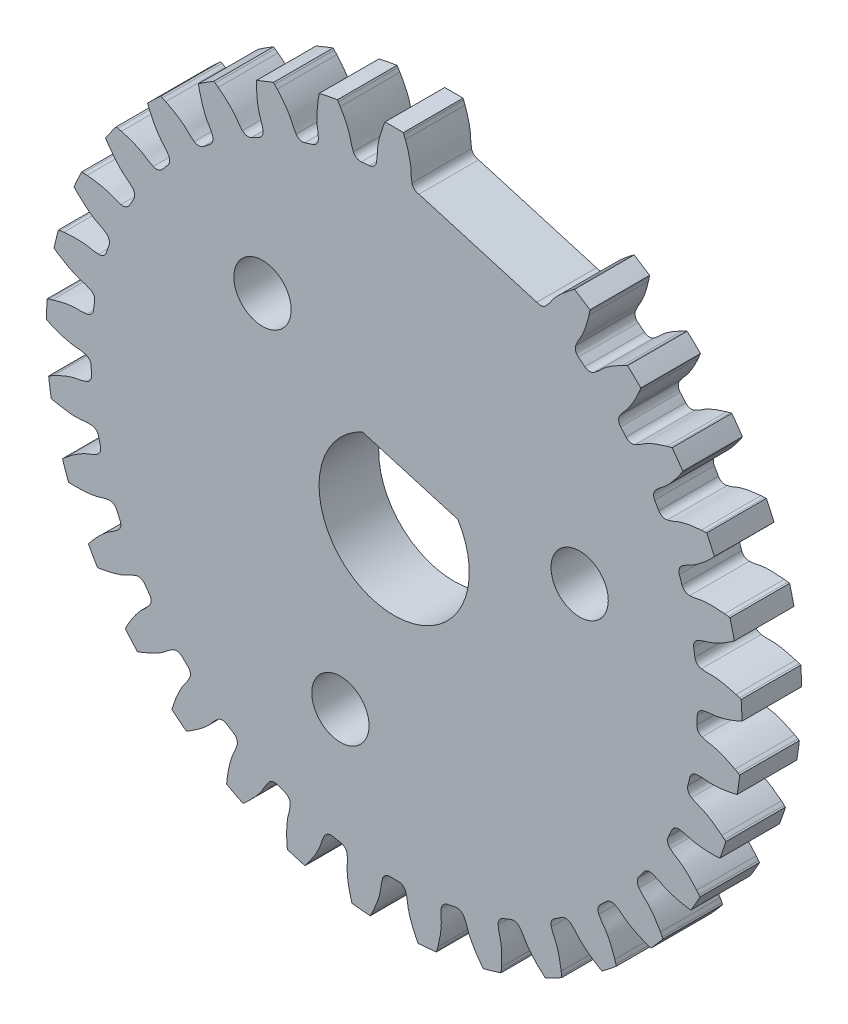
SolidWorks part; units mm, degrees
ref_plane "Front Plane" through (0, 0, 0) normal (0, 0, 1) x (1, 0, 0)
ref_plane "Top Plane" through (0, 0, 0) normal (0, 1, 0) x (1, 0, 0)
ref_plane "Right Plane" through (0, 0, 0) normal (1, 0, 0) x (0, 0, -1)
sketch "Sketch1" plane through (0, 0, 0) normal (0, 0, 1) x (1, 0, 0)
  line L0 (1.3177, 16.0878) -> (7.5892, 14.2464)
  line L1 (-1.6934, 3.6239) -> (3.3838, 2.1331)
  line L2 (-2.8624, -9.7484) -> (4.4535, 15.1671) construction
  arc A0 (-1.6934, 3.6239) -> (3.3838, 2.1331) centre (0, 0) ccw
  circle A1 centre (-2.8624, -9.7484) radius 1.524
  arc A2 (0.9461, 16.421) -> (1.3177, 16.0878) centre (1.3514, 16.4992) ccw
  circle A3 centre (-7.0112, 7.3531) radius 1.524
  arc A4 (7.5892, 14.2464) -> (8.0819, 14.3257) centre (7.7833, 14.6106) ccw
  arc A5 (9.6738, 13.3027) -> (9.8063, 12.8215) centre (10.057, 13.1494) ccw
  arc A6 (10.1482, 12.5526) -> (9.8063, 12.8215) centre (0, 0) ccw
  arc A7 (10.1482, 12.5526) -> (10.647, 12.5373) centre (10.4077, 12.8736) ccw
  arc A8 (12.0165, 11.2315) -> (12.0556, 10.734) centre (12.3638, 11.0084) ccw
  arc A9 (12.3404, 10.4052) -> (12.0556, 10.734) centre (0, 0) ccw
  arc A10 (12.3404, 10.4052) -> (12.8273, 10.2958) centre (12.6559, 10.6713) ccw
  arc A11 (13.925, 8.7544) -> (13.8691, 8.2585) centre (14.2237, 8.4696) ccw
  arc A12 (14.0866, 7.8818) -> (13.8691, 8.2585) centre (0, 0) ccw
  arc A13 (14.0866, 7.8818) -> (14.544, 7.6822) centre (14.4468, 8.0833) ccw
  arc A14 (15.3301, 5.9609) -> (15.1814, 5.4845) centre (15.5696, 5.6247) ccw
  arc A15 (15.3237, 5.0734) -> (15.1814, 5.4845) centre (0, 0) ccw
  arc A16 (15.3237, 5.0734) -> (15.735, 4.7909) centre (15.7155, 5.2032) ccw
  arc A17 (16.1812, 2.9519) -> (15.945, 2.5123) centre (16.3527, 2.5765) ccw
  arc A18 (16.0069, 2.0817) -> (15.945, 2.5123) centre (0, 0) ccw
  arc A19 (16.0069, 2.0817) -> (16.3574, 1.7264) centre (16.4162, 2.135) ccw
  arc A20 (16.4474, -0.1637) -> (16.1323, -0.5507) centre (16.5448, -0.5648) ccw
  arc A21 (16.1116, -0.9852) -> (16.1323, -0.5507) centre (0, 0) ccw
  arc A22 (16.1116, -0.9852) -> (16.3885, -1.4004) centre (16.5236, -1.0104) ccw
  arc A23 (16.1192, -3.2735) -> (15.7365, -3.5938) centre (16.1389, -3.6857) ccw
  arc A24 (15.634, -4.0166) -> (15.7365, -3.5938) centre (0, 0) ccw
  arc A25 (15.634, -4.0166) -> (15.8273, -4.4767) centre (16.0338, -4.1193) ccw
  arc A26 (15.2084, -6.2649) -> (14.772, -6.5071) centre (15.1497, -6.6734) ccw
  arc A27 (14.5913, -6.9027) -> (14.772, -6.5071) centre (0, 0) ccw
  arc A28 (14.5913, -6.9027) -> (14.6941, -7.3911) centre (14.9644, -7.0792) ccw
  arc A29 (13.7479, -9.0299) -> (13.2736, -9.1851) centre (13.613, -9.42) ccw
  arc A30 (13.0213, -9.5394) -> (13.2736, -9.1851) centre (0, 0) ccw
  arc A31 (13.0213, -9.5394) -> (13.0297, -10.0384) centre (13.3543, -9.7833) ccw
  arc A32 (11.7906, -11.4685) -> (11.2954, -11.5312) centre (11.5843, -11.826) ccw
  arc A33 (10.9806, -11.8313) -> (11.2954, -11.5312) centre (0, 0) ccw
  arc A34 (10.9806, -11.8313) -> (10.8945, -12.3229) centre (11.2614, -12.1339) ccw
  arc A35 (9.4071, -13.4926) -> (8.909, -13.4604) centre (9.1368, -13.8046) ccw
  arc A36 (8.5431, -13.6956) -> (8.909, -13.4604) centre (0, 0) ccw
  arc A37 (8.5431, -13.6956) -> (8.3655, -14.162) centre (8.7616, -14.0458) ccw
  arc A38 (6.6836, -15.0291) -> (6.2006, -14.9032) centre (6.3592, -15.2843) ccw
  arc A39 (5.7968, -15.0649) -> (6.2006, -14.9032) centre (0, 0) ccw
  arc A40 (5.7968, -15.0649) -> (5.5341, -15.4893) centre (5.945, -15.4501) ccw
  arc A41 (3.7185, -16.0224) -> (3.2681, -15.8074) centre (3.3517, -16.2116) ccw
  arc A42 (2.841, -15.8897) -> (3.2681, -15.8074) centre (0, 0) ccw
  arc A43 (2.841, -15.8897) -> (2.5028, -16.2567) centre (2.9136, -16.296) ccw
  arc A44 (0.6191, -16.4366) -> (0.2175, -16.1402) centre (0.2231, -16.5529) ccw
  arc A45 (-0.2175, -16.1402) -> (0.2175, -16.1402) centre (0, 0) ccw
  arc A46 (-0.2175, -16.1402) -> (-0.6191, -16.4366) centre (-0.2231, -16.5529) ccw
  arc A47 (-2.5028, -16.2567) -> (-2.841, -15.8897) centre (-2.9136, -16.296) ccw
  arc A48 (-3.2681, -15.8074) -> (-2.841, -15.8897) centre (0, 0) ccw
  arc A49 (-3.2681, -15.8074) -> (-3.7185, -16.0224) centre (-3.3517, -16.2116) ccw
  arc A50 (-5.5341, -15.4893) -> (-5.7968, -15.0649) centre (-5.945, -15.4501) ccw
  arc A51 (-6.2006, -14.9032) -> (-5.7968, -15.0649) centre (0, 0) ccw
  arc A52 (-6.2006, -14.9032) -> (-6.6836, -15.0291) centre (-6.3592, -15.2843) ccw
  arc A53 (-8.3655, -14.162) -> (-8.5431, -13.6956) centre (-8.7616, -14.0458) ccw
  arc A54 (-8.909, -13.4604) -> (-8.5431, -13.6956) centre (0, 0) ccw
  arc A55 (-8.909, -13.4604) -> (-9.4071, -13.4926) centre (-9.1368, -13.8046) ccw
  arc A56 (-10.8945, -12.3229) -> (-10.9806, -11.8313) centre (-11.2614, -12.1339) ccw
  arc A57 (-11.2954, -11.5312) -> (-10.9806, -11.8313) centre (0, 0) ccw
  arc A58 (-11.2954, -11.5312) -> (-11.7906, -11.4685) centre (-11.5843, -11.826) ccw
  arc A59 (-13.0297, -10.0384) -> (-13.0213, -9.5394) centre (-13.3543, -9.7833) ccw
  arc A60 (-13.2736, -9.1851) -> (-13.0213, -9.5394) centre (0, 0) ccw
  arc A61 (-13.2736, -9.1851) -> (-13.7479, -9.0299) centre (-13.613, -9.42) ccw
  arc A62 (-14.6941, -7.3911) -> (-14.5913, -6.9027) centre (-14.9644, -7.0792) ccw
  arc A63 (-14.772, -6.5071) -> (-14.5913, -6.9027) centre (0, 0) ccw
  arc A64 (-14.772, -6.5071) -> (-15.2084, -6.2649) centre (-15.1497, -6.6734) ccw
  arc A65 (-15.8273, -4.4767) -> (-15.634, -4.0166) centre (-16.0338, -4.1193) ccw
  arc A66 (-15.7365, -3.5938) -> (-15.634, -4.0166) centre (0, 0) ccw
  arc A67 (-15.7365, -3.5938) -> (-16.1192, -3.2735) centre (-16.1389, -3.6857) ccw
  arc A68 (-16.3885, -1.4004) -> (-16.1116, -0.9852) centre (-16.5236, -1.0104) ccw
  arc A69 (-16.1323, -0.5507) -> (-16.1116, -0.9852) centre (0, 0) ccw
  arc A70 (-16.1323, -0.5507) -> (-16.4474, -0.1637) centre (-16.5448, -0.5648) ccw
  arc A71 (-16.3574, 1.7264) -> (-16.0069, 2.0817) centre (-16.4162, 2.135) ccw
  arc A72 (-15.945, 2.5123) -> (-16.0069, 2.0817) centre (0, 0) ccw
  arc A73 (-15.945, 2.5123) -> (-16.1812, 2.9519) centre (-16.3527, 2.5765) ccw
  arc A74 (-15.735, 4.7909) -> (-15.3237, 5.0734) centre (-15.7155, 5.2032) ccw
  arc A75 (-15.1814, 5.4845) -> (-15.3237, 5.0734) centre (0, 0) ccw
  arc A76 (-15.1814, 5.4845) -> (-15.3301, 5.9609) centre (-15.5696, 5.6247) ccw
  arc A77 (-14.544, 7.6822) -> (-14.0866, 7.8818) centre (-14.4468, 8.0833) ccw
  arc A78 (-13.8691, 8.2585) -> (-14.0866, 7.8818) centre (0, 0) ccw
  arc A79 (-13.8691, 8.2585) -> (-13.925, 8.7544) centre (-14.2237, 8.4696) ccw
  arc A80 (-12.8273, 10.2958) -> (-12.3404, 10.4052) centre (-12.6559, 10.6713) ccw
  arc A81 (-12.0556, 10.734) -> (-12.3404, 10.4052) centre (0, 0) ccw
  arc A82 (-12.0556, 10.734) -> (-12.0165, 11.2315) centre (-12.3638, 11.0084) ccw
  arc A83 (-10.647, 12.5373) -> (-10.1482, 12.5526) centre (-10.4077, 12.8736) ccw
  arc A84 (-9.8063, 12.8215) -> (-10.1482, 12.5526) centre (0, 0) ccw
  arc A85 (-9.8063, 12.8215) -> (-9.6738, 13.3027) centre (-10.057, 13.1494) ccw
  arc A86 (-8.0819, 14.3257) -> (-7.5892, 14.2464) centre (-7.7833, 14.6106) ccw
  arc A87 (-7.2026, 14.4457) -> (-7.5892, 14.2464) centre (0, 0) ccw
  arc A88 (-7.2026, 14.4457) -> (-6.9814, 14.8931) centre (-7.3867, 14.8151) ccw
  arc A89 (-5.2247, 15.5964) -> (-4.7559, 15.4252) centre (-4.8775, 15.8196) ccw
  arc A90 (-4.3386, 15.5477) -> (-4.7559, 15.4252) centre (0, 0) ccw
  arc A91 (-4.3386, 15.5477) -> (-4.0367, 15.9452) centre (-4.4495, 15.9453) ccw
  arc A92 (-2.1786, 16.3033) -> (-1.7507, 16.0465) centre (-1.7955, 16.4568) ccw
  arc A93 (-1.3177, 16.0878) -> (-1.7507, 16.0465) centre (0, 0) ccw
  arc A94 (-1.3177, 16.0878) -> (-0.9461, 16.421) centre (-1.3514, 16.4992) ccw
  arc A95 (10.4216, 15.3105) -> (9.5977, 15.84) centre (0, 0) ccw
  arc A96 (-14.3129, -11.7542) -> (-13.6715, -12.4944) centre (0, 0) ccw
  arc A97 (-16.6378, 8.1366) -> (-17.0447, 7.2457) centre (0, 0) ccw
  arc A98 (17.0447, 7.2457) -> (16.6378, 8.1366) centre (0, 0) ccw
  arc A99 (11.0599, -14.856) -> (11.8297, -14.2506) centre (0, 0) ccw
  arc A100 (-18.3956, -2.1502) -> (-18.2562, -3.1196) centre (0, 0) ccw
  arc A101 (17.3359, -6.5182) -> (17.6562, -5.5927) centre (0, 0) ccw
  arc A102 (4.7462, -17.9024) -> (5.6859, -17.6264) centre (0, 0) ccw
  arc A103 (18.1079, 3.889) -> (17.877, 4.8408) centre (0, 0) ccw
  arc A104 (-12.422, 13.7374) -> (-13.1308, 13.0615) centre (0, 0) ccw
  arc A105 (-17.877, 4.8408) -> (-18.1079, 3.889) centre (0, 0) ccw
  arc A106 (-9.5977, 15.84) -> (-10.4216, 15.3105) centre (0, 0) ccw
  arc A107 (-5.6859, -17.6264) -> (-4.7462, -17.9024) centre (0, 0) ccw
  arc A108 (0.4897, 18.5144) -> (-0.4897, 18.5144) centre (0, 0) ccw
  arc A109 (-11.8297, -14.2506) -> (-11.0599, -14.856) centre (0, 0) ccw
  arc A110 (-16.2787, -8.8331) -> (-15.7891, -9.6813) centre (0, 0) ccw
  arc A111 (1.2724, -18.4771) -> (2.2474, -18.384) centre (0, 0) ccw
  arc A112 (-3.023, 18.2725) -> (-3.9847, 18.0871) centre (0, 0) ccw
  arc A113 (18.5167, 0.3918) -> (18.4701, 1.3701) centre (0, 0) ccw
  arc A114 (13.1308, 13.0615) -> (12.422, 13.7374) centre (0, 0) ccw
  arc A115 (8.0485, -16.6806) -> (8.919, -16.2318) centre (0, 0) ccw
  arc A116 (13.6715, -12.4944) -> (14.3129, -11.7542) centre (0, 0) ccw
  arc A117 (-18.4701, 1.3701) -> (-18.5167, 0.3918) centre (0, 0) ccw
  arc A118 (-2.2474, -18.384) -> (-1.2724, -18.4771) centre (0, 0) ccw
  arc A119 (15.3654, 10.3405) -> (14.7973, 11.1383) centre (0, 0) ccw
  arc A120 (-8.919, -16.2318) -> (-8.0485, -16.6806) centre (0, 0) ccw
  arc A121 (15.7891, -9.6813) -> (16.2787, -8.8331) centre (0, 0) ccw
  arc A122 (-14.7973, 11.1383) -> (-15.3654, 10.3405) centre (0, 0) ccw
  arc A123 (-17.6562, -5.5927) -> (-17.3359, -6.5182) centre (0, 0) ccw
  arc A124 (18.2562, -3.1196) -> (18.3956, -2.1502) centre (0, 0) ccw
  arc A125 (-6.4265, 17.3701) -> (-7.3357, 17.0061) centre (0, 0) ccw
  circle A126 centre (9.8736, 2.3953) radius 1.524
  spline S31 degree 3 poles (-11.7906, -11.4685) (-11.8581, -11.5075) (-11.9247, -11.5479) (-12.0526, -11.6363) (-12.1128, -11.6859) (-12.2326, -11.7859) (-12.2929, -11.8353) (-12.421, -11.9234) (-12.4877, -11.9637) (-12.8258, -12.1584) (-13.1079, -12.2893) (-13.4001, -12.3987) knots 0 0 0 0 0.125 0.125 0.25 0.25 0.375 0.375 0.5 0.5 1 1 1 1
  spline S32 degree 3 poles (-6.6836, -15.0291) (-6.7318, -15.0904) (-6.7786, -15.1527) (-6.8644, -15.2823) (-6.9019, -15.3507) (-6.9759, -15.4881) (-7.0136, -15.5563) (-7.0998, -15.6857) (-7.1467, -15.7479) (-7.3882, -16.0543) (-7.6014, -16.2807) (-7.8321, -16.4909) knots 0 0 0 0 0.125 0.125 0.25 0.25 0.375 0.375 0.5 0.5 1 1 1 1
  spline S33 degree 3 poles (-3.7185, -16.0224) (-3.7543, -16.0917) (-3.7885, -16.1617) (-3.8482, -16.3052) (-3.872, -16.3795) (-3.9187, -16.5284) (-3.9428, -16.6025) (-4.0029, -16.7459) (-4.0372, -16.8158) (-4.2164, -17.1624) (-4.3829, -17.4251) (-4.5696, -17.6751) knots 0 0 0 0 0.125 0.125 0.25 0.25 0.375 0.375 0.5 0.5 1 1 1 1
  spline S34 degree 3 poles (-16.1812, 2.9519) (-16.2521, 2.9843) (-16.3237, 3.0152) (-16.4699, 3.068) (-16.5452, 3.0883) (-16.6961, 3.1278) (-16.7713, 3.1484) (-16.9174, 3.2016) (-16.9889, 3.2325) (-17.3436, 3.395) (-17.6139, 3.5488) (-17.8725, 3.7234) knots 0 0 0 0 0.125 0.125 0.25 0.25 0.375 0.375 0.5 0.5 1 1 1 1
  spline S35 degree 3 poles (-4.0367, 15.9452) (-4.0367, 16.0232) (-4.0384, 16.1011) (-4.0511, 16.256) (-4.0639, 16.3329) (-4.0906, 16.4867) (-4.1032, 16.5636) (-4.1155, 16.7186) (-4.117, 16.7965) (-4.1166, 17.1866) (-4.0889, 17.4964) (-4.0376, 17.8042) knots 0 0 0 0 0.125 0.125 0.25 0.25 0.375 0.375 0.5 0.5 1 1 1 1
  spline S36 degree 3 poles (-16.1192, -3.2735) (-16.1971, -3.2697) (-16.275, -3.2677) (-16.4304, -3.273) (-16.5078, -3.2821) (-16.6626, -3.3015) (-16.7401, -3.3104) (-16.8955, -3.3153) (-16.9733, -3.3132) (-17.363, -3.2941) (-17.6712, -3.2518) (-17.9761, -3.1858) knots 0 0 0 0 0.125 0.125 0.25 0.25 0.375 0.375 0.5 0.5 1 1 1 1
  spline S37 degree 3 poles (-16.4474, -0.1637) (-16.5232, -0.1453) (-16.5993, -0.1286) (-16.7529, -0.1044) (-16.8306, -0.0987) (-16.9863, -0.0884) (-17.0641, -0.0825) (-17.2176, -0.0579) (-17.2936, -0.0411) (-17.6727, 0.0514) (-17.9672, 0.1513) (-18.2542, 0.2737) knots 0 0 0 0 0.125 0.125 0.25 0.25 0.375 0.375 0.5 0.5 1 1 1 1
  spline S38 degree 3 poles (-15.3301, 5.9609) (-15.3936, 6.0062) (-15.4581, 6.0499) (-15.5916, 6.1295) (-15.6617, 6.1637) (-15.8024, 6.2311) (-15.8724, 6.2655) (-16.0058, 6.3454) (-16.0701, 6.3893) (-16.3876, 6.616) (-16.624, 6.8182) (-16.8449, 7.0385) knots 0 0 0 0 0.125 0.125 0.25 0.25 0.375 0.375 0.5 0.5 1 1 1 1
  spline S39 degree 3 poles (5.5341, -15.4893) (5.5415, -15.5669) (5.5506, -15.6443) (5.578, -15.7973) (5.598, -15.8727) (5.6393, -16.0232) (5.6591, -16.0986) (5.686, -16.2517) (5.695, -16.3291) (5.7316, -16.7175) (5.7336, -17.0285) (5.7117, -17.3398) knots 0 0 0 0 0.125 0.125 0.25 0.25 0.375 0.375 0.5 0.5 1 1 1 1
  spline S40 degree 3 poles (14.6941, -7.3911) (14.753, -7.4422) (14.813, -7.4919) (14.9384, -7.5838) (15.0049, -7.6245) (15.1386, -7.705) (15.205, -7.7459) (15.3301, -7.8381) (15.39, -7.8879) (15.6846, -8.1438) (15.9006, -8.3675) (16.0995, -8.6079) knots 0 0 0 0 0.125 0.125 0.25 0.25 0.375 0.375 0.5 0.5 1 1 1 1
  spline S41 degree 3 poles (2.5028, -16.2567) (2.4953, -16.3344) (2.4896, -16.412) (2.4875, -16.5675) (2.493, -16.6453) (2.505, -16.8009) (2.5102, -16.8786) (2.5076, -17.0341) (2.5018, -17.1118) (2.4642, -17.5001) (2.4073, -17.8059) (2.3269, -18.1074) knots 0 0 0 0 0.125 0.125 0.25 0.25 0.375 0.375 0.5 0.5 1 1 1 1
  spline S42 degree 3 poles (12.8273, 10.2958) (12.8983, 10.3282) (12.9684, 10.3621) (13.1041, 10.438) (13.1688, 10.4816) (13.2975, 10.5698) (13.3623, 10.6132) (13.4981, 10.6887) (13.5683, 10.7225) (13.9234, 10.8841) (14.2167, 10.9877) (14.518, 11.0688) knots 0 0 0 0 0.125 0.125 0.25 0.25 0.375 0.375 0.5 0.5 1 1 1 1
  spline S43 degree 3 poles (8.3655, -14.162) (8.3875, -14.2369) (8.411, -14.3111) (8.4668, -14.4562) (8.5008, -14.5264) (8.5698, -14.6664) (8.6035, -14.7367) (8.6589, -14.8819) (8.6824, -14.9562) (8.7918, -15.3307) (8.8526, -15.6357) (8.89, -15.9455) knots 0 0 0 0 0.125 0.125 0.25 0.25 0.375 0.375 0.5 0.5 1 1 1 1
  spline S44 degree 3 poles (-13.925, 8.7544) (-13.9788, 8.8109) (-14.0338, 8.8661) (-14.1498, 8.9695) (-14.2122, 9.0163) (-14.3376, 9.1091) (-14.3998, 9.1561) (-14.5157, 9.2598) (-14.5705, 9.3151) (-14.8394, 9.5978) (-15.0332, 9.8411) (-15.2084, 10.0992) knots 0 0 0 0 0.125 0.125 0.25 0.25 0.375 0.375 0.5 0.5 1 1 1 1
  spline S45 degree 3 poles (10.647, 12.5373) (10.7106, 12.5826) (10.773, 12.6291) (10.8919, 12.7293) (10.9471, 12.7844) (11.0568, 12.8953) (11.1122, 12.9502) (11.2314, 13.0501) (11.2939, 13.0966) (11.612, 13.3225) (11.8803, 13.4797) (12.1608, 13.6163) knots 0 0 0 0 0.125 0.125 0.25 0.25 0.375 0.375 0.5 0.5 1 1 1 1
  spline S46 degree 3 poles (-0.6191, -16.4366) (-0.6411, -16.5114) (-0.6614, -16.5866) (-0.6929, -16.7389) (-0.7022, -16.8163) (-0.7199, -16.9713) (-0.7295, -17.0487) (-0.7614, -17.2008) (-0.7818, -17.276) (-0.8922, -17.6502) (-1.006, -17.9397) (-1.142, -18.2205) knots 0 0 0 0 0.125 0.125 0.25 0.25 0.375 0.375 0.5 0.5 1 1 1 1
  spline S47 degree 3 poles (15.735, 4.7909) (15.813, 4.7946) (15.8907, 4.8) (16.0449, 4.82) (16.1211, 4.8365) (16.2734, 4.8705) (16.3496, 4.8867) (16.5038, 4.9063) (16.5816, 4.9116) (16.9713, 4.9297) (17.282, 4.9168) (17.5919, 4.8802) knots 0 0 0 0 0.125 0.125 0.25 0.25 0.375 0.375 0.5 0.5 1 1 1 1
  spline S48 degree 3 poles (-6.9814, 14.8931) (-6.9962, 14.9697) (-7.0126, 15.0458) (-7.0543, 15.1956) (-7.0815, 15.2687) (-7.1368, 15.4146) (-7.1637, 15.4877) (-7.2051, 15.6376) (-7.2214, 15.7138) (-7.2948, 16.097) (-7.3263, 16.4064) (-7.3341, 16.7183) knots 0 0 0 0 0.125 0.125 0.25 0.25 0.375 0.375 0.5 0.5 1 1 1 1
  spline S49 degree 3 poles (-13.7479, -9.0299) (-13.8217, -9.0554) (-13.8947, -9.0825) (-14.037, -9.1451) (-14.1055, -9.1824) (-14.242, -9.2579) (-14.3106, -9.295) (-14.453, -9.3572) (-14.5261, -9.3842) (-14.895, -9.5113) (-15.1968, -9.5866) (-15.5044, -9.6387) knots 0 0 0 0 0.125 0.125 0.25 0.25 0.375 0.375 0.5 0.5 1 1 1 1
  spline S50 degree 3 poles (16.3885, -1.4004) (16.4622, -1.426) (16.5364, -1.4498) (16.6869, -1.4886) (16.7638, -1.5016) (16.9178, -1.5266) (16.9947, -1.5399) (17.1451, -1.579) (17.2192, -1.603) (17.5878, -1.731) (17.8715, -1.8585) (18.1455, -2.0077) knots 0 0 0 0 0.125 0.125 0.25 0.25 0.375 0.375 0.5 0.5 1 1 1 1
  spline S51 degree 3 poles (14.544, 7.6822) (14.6198, 7.7005) (14.6951, 7.7206) (14.8427, 7.7694) (14.9144, 7.8) (15.0575, 7.8622) (15.1293, 7.8926) (15.2771, 7.941) (15.3524, 7.9609) (15.7316, 8.0524) (16.0392, 8.0986) (16.3504, 8.1213) knots 0 0 0 0 0.125 0.125 0.25 0.25 0.375 0.375 0.5 0.5 1 1 1 1
  spline S52 degree 3 poles (16.3574, 1.7264) (16.4346, 1.7153) (16.5119, 1.7059) (16.6671, 1.6964) (16.745, 1.6981) (16.901, 1.7027) (16.979, 1.7042) (17.1341, 1.6943) (17.2114, 1.6847) (17.5975, 1.6288) (17.9002, 1.5573) (18.1976, 1.4627) knots 0 0 0 0 0.125 0.125 0.25 0.25 0.375 0.375 0.5 0.5 1 1 1 1
  spline S53 degree 3 poles (-9.4071, -13.4926) (-9.466, -13.5437) (-9.5238, -13.596) (-9.6326, -13.707) (-9.6823, -13.7671) (-9.781, -13.888) (-9.8309, -13.9479) (-9.94, -14.0586) (-9.9978, -14.1108) (-10.293, -14.3659) (-10.5452, -14.5479) (-10.8114, -14.7107) knots 0 0 0 0 0.125 0.125 0.25 0.25 0.375 0.375 0.5 0.5 1 1 1 1
  spline S54 degree 3 poles (-9.6738, 13.3027) (-9.7028, 13.3751) (-9.7333, 13.4468) (-9.8026, 13.5859) (-9.8431, 13.6526) (-9.9251, 13.7854) (-9.9654, 13.8521) (-10.0343, 13.9914) (-10.0647, 14.0632) (-10.2093, 14.4255) (-10.2988, 14.7234) (-10.3655, 15.0282) knots 0 0 0 0 0.125 0.125 0.25 0.25 0.375 0.375 0.5 0.5 1 1 1 1
  spline S55 degree 3 poles (13.0297, -10.0384) (13.078, -10.0998) (13.1274, -10.1599) (13.2332, -10.2739) (13.2908, -10.3264) (13.4068, -10.4307) (13.4643, -10.4834) (13.5697, -10.5977) (13.6191, -10.6579) (13.8599, -10.9649) (14.0297, -11.2255) (14.1796, -11.4992) knots 0 0 0 0 0.125 0.125 0.25 0.25 0.375 0.375 0.5 0.5 1 1 1 1
  spline S56 degree 3 poles (-12.0165, 11.2315) (-12.0587, 11.2972) (-12.1022, 11.3618) (-12.1967, 11.4853) (-12.249, 11.543) (-12.3546, 11.6579) (-12.4068, 11.7158) (-12.5009, 11.8396) (-12.5443, 11.9043) (-12.7549, 12.2327) (-12.8991, 12.5083) (-13.0223, 12.7949) knots 0 0 0 0 0.125 0.125 0.25 0.25 0.375 0.375 0.5 0.5 1 1 1 1
  spline S57 degree 3 poles (-15.2084, -6.2649) (-15.2856, -6.276) (-15.3625, -6.2887) (-15.514, -6.3233) (-15.5883, -6.347) (-15.7367, -6.3953) (-15.8111, -6.4187) (-15.9627, -6.4529) (-16.0396, -6.4655) (-16.4258, -6.5206) (-16.7364, -6.5373) (-17.0483, -6.5303) knots 0 0 0 0 0.125 0.125 0.25 0.25 0.375 0.375 0.5 0.5 1 1 1 1
  spline S58 degree 3 poles (15.8273, -4.4767) (15.8949, -4.5157) (15.9631, -4.5532) (16.1037, -4.6197) (16.1767, -4.647) (16.3232, -4.7007) (16.3961, -4.7283) (16.5365, -4.7952) (16.6047, -4.8328) (16.9423, -5.0283) (17.1968, -5.2071) (17.4377, -5.4054) knots 0 0 0 0 0.125 0.125 0.25 0.25 0.375 0.375 0.5 0.5 1 1 1 1
  spline S59 degree 3 poles (10.8945, -12.3229) (10.9302, -12.3923) (10.9674, -12.4607) (11.0497, -12.5926) (11.0963, -12.6551) (11.1905, -12.7795) (11.237, -12.8421) (11.3189, -12.9743) (11.356, -13.0428) (11.5343, -13.3898) (11.6517, -13.6778) (11.7471, -13.9749) knots 0 0 0 0 0.125 0.125 0.25 0.25 0.375 0.375 0.5 0.5 1 1 1 1
  spline S60 degree 3 poles (8.0819, 14.3257) (8.1358, 14.3822) (8.1883, 14.4397) (8.286, 14.5606) (8.3298, 14.6251) (8.4166, 14.7548) (8.4606, 14.8192) (8.5586, 14.9398) (8.6113, 14.9973) (8.8808, 15.2793) (9.1146, 15.4844) (9.3642, 15.6717) knots 0 0 0 0 0.125 0.125 0.25 0.25 0.375 0.375 0.5 0.5 1 1 1 1
  spline S61 degree 3 poles (-6.229, 17.1607) (-6.0194, 16.9296) (-5.8286, 16.6837) (-5.6173, 16.3559) (-5.5766, 16.2895) (-5.5031, 16.1525) (-5.4721, 16.081) (-5.4115, 15.9372) (-5.3807, 15.8656) (-5.3076, 15.7284) (-5.2669, 15.662) (-5.2247, 15.5964) knots 0 0 0 0 0.5 0.5 0.625 0.625 0.75 0.75 0.875 0.875 1 1 1 1
  spline S62 degree 3 poles (-9.3642, 15.6717) (-9.1146, 15.4844) (-8.8807, 15.2792) (-8.6112, 14.9972) (-8.5586, 14.9398) (-8.4605, 14.8191) (-8.4165, 14.7548) (-8.3298, 14.6251) (-8.286, 14.5606) (-8.1883, 14.4397) (-8.1358, 14.3822) (-8.0819, 14.3257) knots 0 0 0 0 0.5 0.5 0.625 0.625 0.75 0.75 0.875 0.875 1 1 1 1
  spline S63 degree 3 poles (-11.7471, -13.9749) (-11.6517, -13.6778) (-11.5342, -13.3896) (-11.3559, -13.0427) (-11.3188, -12.9742) (-11.2369, -12.8421) (-11.1905, -12.7795) (-11.0963, -12.6551) (-11.0497, -12.5926) (-10.9674, -12.4607) (-10.9302, -12.3922) (-10.8945, -12.3229) knots 0 0 0 0 0.5 0.5 0.625 0.625 0.75 0.75 0.875 0.875 1 1 1 1
  spline S64 degree 3 poles (-8.89, -15.9455) (-8.8526, -15.6357) (-8.7918, -15.3305) (-8.6824, -14.9561) (-8.6589, -14.8818) (-8.6035, -14.7366) (-8.5697, -14.6663) (-8.5008, -14.5264) (-8.4668, -14.4562) (-8.411, -14.3111) (-8.3875, -14.2369) (-8.3655, -14.162) knots 0 0 0 0 0.5 0.5 0.625 0.625 0.75 0.75 0.875 0.875 1 1 1 1
  spline S65 degree 3 poles (-16.0995, -8.6079) (-15.9006, -8.3675) (-15.6844, -8.1436) (-15.39, -7.8878) (-15.3301, -7.838) (-15.2049, -7.7458) (-15.1385, -7.705) (-15.0049, -7.6245) (-14.9383, -7.5838) (-14.813, -7.4919) (-14.753, -7.4422) (-14.6941, -7.3911) knots 0 0 0 0 0.5 0.5 0.625 0.625 0.75 0.75 0.875 0.875 1 1 1 1
  spline S66 degree 3 poles (16.8449, 7.0385) (16.624, 6.8182) (16.3875, 6.6159) (16.0701, 6.3892) (16.0057, 6.3453) (15.8724, 6.2654) (15.8024, 6.2311) (15.6617, 6.1637) (15.5916, 6.1295) (15.458, 6.0499) (15.3936, 6.0061) (15.3301, 5.9609) knots 0 0 0 0 0.5 0.5 0.625 0.625 0.75 0.75 0.875 0.875 1 1 1 1
  spline S67 degree 3 poles (-14.518, 11.0688) (-14.2167, 10.9877) (-13.9233, 10.8841) (-13.5683, 10.7225) (-13.4981, 10.6887) (-13.3622, 10.6132) (-13.2975, 10.5698) (-13.1687, 10.4816) (-13.1041, 10.438) (-12.9684, 10.3621) (-12.8983, 10.3282) (-12.8273, 10.2958) knots 0 0 0 0 0.5 0.5 0.625 0.625 0.75 0.75 0.875 0.875 1 1 1 1
  spline S68 degree 3 poles (-5.7117, -17.3398) (-5.7336, -17.0285) (-5.7316, -16.7173) (-5.695, -16.329) (-5.686, -16.2516) (-5.6591, -16.0985) (-5.6393, -16.0231) (-5.598, -15.8726) (-5.578, -15.7973) (-5.5506, -15.6443) (-5.5415, -15.5669) (-5.5341, -15.4893) knots 0 0 0 0 0.5 0.5 0.625 0.625 0.75 0.75 0.875 0.875 1 1 1 1
  spline S69 degree 3 poles (-14.1796, -11.4992) (-14.0297, -11.2255) (-13.8598, -10.9648) (-13.6191, -10.6579) (-13.5697, -10.5976) (-13.4642, -10.4834) (-13.4068, -10.4307) (-13.2908, -10.3264) (-13.2331, -10.2739) (-13.1274, -10.1599) (-13.078, -10.0997) (-13.0297, -10.0384) knots 0 0 0 0 0.5 0.5 0.625 0.625 0.75 0.75 0.875 0.875 1 1 1 1
  spline S70 degree 3 poles (-17.5919, 4.8802) (-17.282, 4.9168) (-16.9711, 4.9297) (-16.5815, 4.9116) (-16.5038, 4.9063) (-16.3496, 4.8867) (-16.2733, 4.8705) (-16.121, 4.8364) (-16.0448, 4.82) (-15.8907, 4.8) (-15.813, 4.7946) (-15.735, 4.7909) knots 0 0 0 0 0.5 0.5 0.625 0.625 0.75 0.75 0.875 0.875 1 1 1 1
  spline S71 degree 3 poles (7.8321, -16.4909) (7.6014, -16.2807) (7.3881, -16.0542) (7.1466, -15.7478) (7.0997, -15.6857) (7.0136, -15.5563) (6.9759, -15.488) (6.9019, -15.3507) (6.8644, -15.2823) (6.7786, -15.1527) (6.7318, -15.0904) (6.6836, -15.0291) knots 0 0 0 0 0.5 0.5 0.625 0.625 0.75 0.75 0.875 0.875 1 1 1 1
  spline S72 degree 3 poles (-16.3504, 8.1213) (-16.0392, 8.0986) (-15.7315, 8.0524) (-15.3523, 7.9609) (-15.277, 7.941) (-15.1293, 7.8925) (-15.0575, 7.8622) (-14.9144, 7.8) (-14.8427, 7.7694) (-14.6951, 7.7205) (-14.6198, 7.7005) (-14.544, 7.6822) knots 0 0 0 0 0.5 0.5 0.625 0.625 0.75 0.75 0.875 0.875 1 1 1 1
  spline S73 degree 3 poles (10.8114, -14.7107) (10.5452, -14.5479) (10.2929, -14.3658) (9.9978, -14.1107) (9.94, -14.0586) (9.8309, -13.9478) (9.781, -13.8879) (9.6823, -13.7671) (9.6326, -13.707) (9.5238, -13.596) (9.466, -13.5437) (9.4071, -13.4926) knots 0 0 0 0 0.5 0.5 0.625 0.625 0.75 0.75 0.875 0.875 1 1 1 1
  spline S74 degree 3 poles (-17.4377, -5.4054) (-17.1968, -5.2071) (-16.9422, -5.0282) (-16.6046, -4.8327) (-16.5364, -4.7952) (-16.3961, -4.7283) (-16.3231, -4.7007) (-16.1766, -4.647) (-16.1036, -4.6197) (-15.9631, -4.5532) (-15.8948, -4.5157) (-15.8273, -4.4767) knots 0 0 0 0 0.5 0.5 0.625 0.625 0.75 0.75 0.875 0.875 1 1 1 1
  spline S75 degree 3 poles (18.2542, 0.2737) (17.9672, 0.1513) (17.6725, 0.0513) (17.2936, -0.0411) (17.2175, -0.0579) (17.064, -0.0825) (16.9863, -0.0885) (16.8306, -0.0987) (16.7528, -0.1044) (16.5993, -0.1286) (16.5232, -0.1453) (16.4474, -0.1637) knots 0 0 0 0 0.5 0.5 0.625 0.625 0.75 0.75 0.875 0.875 1 1 1 1
  spline S76 degree 3 poles (13.0223, 12.7949) (12.8991, 12.5083) (12.7548, 12.2326) (12.5443, 11.9042) (12.5009, 11.8395) (12.4068, 11.7158) (12.3546, 11.6579) (12.249, 11.543) (12.1966, 11.4852) (12.1022, 11.3617) (12.0587, 11.2971) (12.0165, 11.2315) knots 0 0 0 0 0.5 0.5 0.625 0.625 0.75 0.75 0.875 0.875 1 1 1 1
  spline S77 degree 3 poles (-2.3269, -18.1074) (-2.4073, -17.8059) (-2.4643, -17.4999) (-2.5018, -17.1117) (-2.5076, -17.034) (-2.5102, -16.8786) (-2.505, -16.8008) (-2.493, -16.6452) (-2.4875, -16.5674) (-2.4896, -16.412) (-2.4953, -16.3343) (-2.5028, -16.2567) knots 0 0 0 0 0.5 0.5 0.625 0.625 0.75 0.75 0.875 0.875 1 1 1 1
  spline S78 degree 3 poles (17.9761, -3.1858) (17.6711, -3.2518) (17.3629, -3.2941) (16.9733, -3.3132) (16.8954, -3.3153) (16.74, -3.3104) (16.6626, -3.3015) (16.5078, -3.2821) (16.4303, -3.273) (16.275, -3.2677) (16.1971, -3.2697) (16.1192, -3.2735) knots 0 0 0 0 0.5 0.5 0.625 0.625 0.75 0.75 0.875 0.875 1 1 1 1
  spline S79 degree 3 poles (-18.1976, 1.4627) (-17.9002, 1.5573) (-17.5974, 1.6288) (-17.2113, 1.6848) (-17.134, 1.6943) (-16.9789, 1.7042) (-16.901, 1.7027) (-16.745, 1.6981) (-16.667, 1.6964) (-16.5119, 1.7059) (-16.4346, 1.7153) (-16.3574, 1.7264) knots 0 0 0 0 0.5 0.5 0.625 0.625 0.75 0.75 0.875 0.875 1 1 1 1
  spline S80 degree 3 poles (-12.1608, 13.6163) (-11.8803, 13.4797) (-11.6118, 13.3224) (-11.2938, 13.0965) (-11.2313, 13.0501) (-11.1122, 12.9502) (-11.0568, 12.8953) (-10.9471, 12.7844) (-10.8919, 12.7293) (-10.773, 12.6291) (-10.7106, 12.5826) (-10.647, 12.5373) knots 0 0 0 0 0.5 0.5 0.625 0.625 0.75 0.75 0.875 0.875 1 1 1 1
  spline S81 degree 3 poles (1.142, -18.2205) (1.006, -17.9397) (0.8922, -17.65) (0.7818, -17.2759) (0.7614, -17.2008) (0.7295, -17.0486) (0.7199, -16.9713) (0.7022, -16.8162) (0.6929, -16.7388) (0.6614, -16.5866) (0.641, -16.5114) (0.6191, -16.4366) knots 0 0 0 0 0.5 0.5 0.625 0.625 0.75 0.75 0.875 0.875 1 1 1 1
  spline S82 degree 3 poles (-18.1455, -2.0077) (-17.8715, -1.8585) (-17.5876, -1.731) (-17.2192, -1.603) (-17.1451, -1.579) (-16.9946, -1.5399) (-16.9178, -1.5266) (-16.7638, -1.5016) (-16.6869, -1.4885) (-16.5363, -1.4498) (-16.4622, -1.426) (-16.3885, -1.4004) knots 0 0 0 0 0.5 0.5 0.625 0.625 0.75 0.75 0.875 0.875 1 1 1 1
  spline S83 degree 3 poles (15.2084, 10.0992) (15.0332, 9.8411) (14.8393, 9.5977) (14.5705, 9.315) (14.5156, 9.2598) (14.3998, 9.1561) (14.3376, 9.1091) (14.2122, 9.0163) (14.1498, 8.9694) (14.0337, 8.866) (13.9788, 8.8109) (13.925, 8.7544) knots 0 0 0 0 0.5 0.5 0.625 0.625 0.75 0.75 0.875 0.875 1 1 1 1
  spline S84 degree 3 poles (10.3655, 15.0282) (10.2988, 14.7234) (10.2092, 14.4254) (10.0647, 14.0631) (10.0343, 13.9914) (9.9653, 13.8521) (9.9251, 13.7853) (9.8431, 13.6525) (9.8026, 13.5859) (9.7333, 13.4468) (9.7028, 13.3751) (9.6738, 13.3027) knots 0 0 0 0 0.5 0.5 0.625 0.625 0.75 0.75 0.875 0.875 1 1 1 1
  spline S85 degree 3 poles (4.5696, -17.6751) (4.3829, -17.4251) (4.2163, -17.1622) (4.0372, -16.8158) (4.0029, -16.7458) (3.9428, -16.6025) (3.9187, -16.5283) (3.872, -16.3794) (3.8482, -16.3052) (3.7884, -16.1617) (3.7543, -16.0917) (3.7185, -16.0224) knots 0 0 0 0 0.5 0.5 0.625 0.625 0.75 0.75 0.875 0.875 1 1 1 1
  spline S86 degree 3 poles (0.5951, 18.2465) (0.7038, 17.9541) (0.7896, 17.6549) (0.8639, 17.272) (0.8771, 17.1953) (0.8944, 17.0408) (0.8966, 16.9628) (0.8994, 16.8068) (0.9014, 16.7289) (0.9183, 16.5744) (0.9314, 16.4976) (0.9461, 16.421) knots 0 0 0 0 0.5 0.5 0.625 0.625 0.75 0.75 0.875 0.875 1 1 1 1
  spline S87 degree 3 poles (17.0483, -6.5303) (16.7364, -6.5373) (16.4257, -6.5206) (16.0395, -6.4655) (15.9627, -6.4529) (15.811, -6.4187) (15.7367, -6.3953) (15.5883, -6.3469) (15.514, -6.3233) (15.3624, -6.2887) (15.2856, -6.276) (15.2084, -6.2649) knots 0 0 0 0 0.5 0.5 0.625 0.625 0.75 0.75 0.875 0.875 1 1 1 1
  spline S88 degree 3 poles (15.5044, -9.6387) (15.1968, -9.5866) (14.8948, -9.5113) (14.5261, -9.3842) (14.453, -9.3572) (14.3105, -9.2949) (14.242, -9.2579) (14.1054, -9.1823) (14.0369, -9.1451) (13.8947, -9.0824) (13.8216, -9.0554) (13.7479, -9.0299) knots 0 0 0 0 0.5 0.5 0.625 0.625 0.75 0.75 0.875 0.875 1 1 1 1
  spline S89 degree 3 poles (-2.8688, 18.0294) (-2.7067, 17.7628) (-2.5659, 17.4853) (-2.4205, 17.1234) (-2.393, 17.0505) (-2.3468, 16.9021) (-2.3299, 16.826) (-2.2975, 16.6733) (-2.2809, 16.5972) (-2.235, 16.4486) (-2.2077, 16.3757) (-2.1786, 16.3033) knots 0 0 0 0 0.5 0.5 0.625 0.625 0.75 0.75 0.875 0.875 1 1 1 1
  spline S90 degree 3 poles (13.4001, -12.3987) (13.1079, -12.2893) (12.8256, -12.1583) (12.4876, -11.9637) (12.4209, -11.9234) (12.2929, -11.8353) (12.2325, -11.7859) (12.1127, -11.6859) (12.0526, -11.6363) (11.9247, -11.5479) (11.8581, -11.5075) (11.7906, -11.4685) knots 0 0 0 0 0.5 0.5 0.625 0.625 0.75 0.75 0.875 0.875 1 1 1 1
  spline S91 degree 3 poles (17.8725, 3.7234) (17.6139, 3.5488) (17.3434, 3.3949) (16.9888, 3.2325) (16.9173, 3.2016) (16.7713, 3.1483) (16.6961, 3.1278) (16.5451, 3.0883) (16.4698, 3.068) (16.3236, 3.0151) (16.2521, 2.9843) (16.1812, 2.9519) knots 0 0 0 0 0.5 0.5 0.625 0.625 0.75 0.75 0.875 0.875 1 1 1 1
  spline S92 degree 3 poles (-0.9461, 16.421) (-0.9314, 16.4976) (-0.9183, 16.5744) (-0.9014, 16.7289) (-0.8994, 16.8069) (-0.8966, 16.9629) (-0.8944, 17.0408) (-0.8771, 17.1953) (-0.8639, 17.2721) (-0.7896, 17.6551) (-0.7038, 17.9541) (-0.5951, 18.2465) knots 0 0 0 0 0.125 0.125 0.25 0.25 0.375 0.375 0.5 0.5 1 1 1 1
  spline S93 degree 2 poles (9.5977, 15.84) (9.5691, 15.8203) (9.525, 15.789) knots 0 0 0 0.5 0.5 0.5
  spline S94 degree 3 poles (9.525, 15.789) (9.4809, 15.7578) (9.4224, 15.7155) (9.3642, 15.6717) knots 0.5 0.5 0.5 0.5 1 1 1 1
  spline S95 degree 2 poles (10.4216, 15.3105) (10.4155, 15.2763) (10.4054, 15.2232) knots 0 0 0 0.5 0.5 0.5
  spline S96 degree 3 poles (10.4054, 15.2232) (10.3953, 15.1701) (10.3811, 15.0994) (10.3655, 15.0282) knots 0.5 0.5 0.5 0.5 1 1 1 1
  spline S97 degree 2 poles (-13.6715, -12.4944) (-13.6386, -12.4836) (-13.5874, -12.466) knots 0 0 0 0.5 0.5 0.5
  spline S98 degree 3 poles (-13.5874, -12.466) (-13.5363, -12.4484) (-13.4683, -12.4243) (-13.4001, -12.3987) knots 0.5 0.5 0.5 0.5 1 1 1 1
  spline S99 degree 2 poles (-14.3129, -11.7542) (-14.2975, -11.7231) (-14.2728, -11.6751) knots 0 0 0 0.5 0.5 0.5
  spline S100 degree 3 poles (-14.2728, -11.6751) (-14.2481, -11.627) (-14.2145, -11.5631) (-14.1796, -11.4992) knots 0.5 0.5 0.5 0.5 1 1 1 1
  spline S101 degree 2 poles (-17.0447, 7.2457) (-17.0211, 7.2202) (-16.9839, 7.181) knots 0 0 0 0.5 0.5 0.5
  spline S102 degree 3 poles (-16.9839, 7.181) (-16.9467, 7.1418) (-16.8964, 7.09) (-16.8449, 7.0385) knots 0.5 0.5 0.5 0.5 1 1 1 1
  spline S103 degree 2 poles (-16.6378, 8.1366) (-16.6031, 8.1355) (-16.5491, 8.133) knots 0 0 0 0.5 0.5 0.5
  spline S104 degree 3 poles (-16.5491, 8.133) (-16.4951, 8.1305) (-16.4231, 8.1265) (-16.3504, 8.1213) knots 0.5 0.5 0.5 0.5 1 1 1 1
  spline S105 degree 2 poles (16.6378, 8.1366) (16.6031, 8.1355) (16.5491, 8.133) knots 0 0 0 0.5 0.5 0.5
  spline S106 degree 3 poles (16.5491, 8.133) (16.4951, 8.1305) (16.4231, 8.1265) (16.3504, 8.1213) knots 0.5 0.5 0.5 0.5 1 1 1 1
  spline S107 degree 2 poles (17.0447, 7.2457) (17.0211, 7.2202) (16.9839, 7.181) knots 0 0 0 0.5 0.5 0.5
  spline S108 degree 3 poles (16.9839, 7.181) (16.9467, 7.1418) (16.8964, 7.09) (16.8449, 7.0385) knots 0.5 0.5 0.5 0.5 1 1 1 1
  spline S109 degree 2 poles (11.8297, -14.2506) (11.8205, -14.2171) (11.8053, -14.1652) knots 0 0 0 0.5 0.5 0.5
  spline S110 degree 3 poles (11.8053, -14.1652) (11.7902, -14.1133) (11.7694, -14.0442) (11.7471, -13.9749) knots 0.5 0.5 0.5 0.5 1 1 1 1
  spline S111 degree 2 poles (11.0599, -14.856) (11.0296, -14.8391) (10.9827, -14.8121) knots 0 0 0 0.5 0.5 0.5
  spline S112 degree 3 poles (10.9827, -14.8121) (10.9358, -14.7852) (10.8736, -14.7486) (10.8114, -14.7107) knots 0.5 0.5 0.5 0.5 1 1 1 1
  spline S113 degree 2 poles (-18.2562, -3.1196) (-18.2226, -3.1283) (-18.1701, -3.1411) knots 0 0 0 0.5 0.5 0.5
  spline S114 degree 3 poles (-18.1701, -3.1411) (-18.1176, -3.154) (-18.0473, -3.1704) (-17.9761, -3.1858) knots 0.5 0.5 0.5 0.5 1 1 1 1
  spline S115 degree 2 poles (-18.3956, -2.1502) (-18.3658, -2.1323) (-18.319, -2.1052) knots 0 0 0 0.5 0.5 0.5
  spline S116 degree 3 poles (-18.319, -2.1052) (-18.2723, -2.0781) (-18.2095, -2.0425) (-18.1455, -2.0077) knots 0.5 0.5 0.5 0.5 1 1 1 1
  spline S117 degree 2 poles (17.6562, -5.5927) (17.6304, -5.5695) (17.5896, -5.5341) knots 0 0 0 0.5 0.5 0.5
  spline S118 degree 3 poles (17.5896, -5.5341) (17.5488, -5.4986) (17.4939, -5.4518) (17.4377, -5.4054) knots 0.5 0.5 0.5 0.5 1 1 1 1
  spline S119 degree 2 poles (17.3359, -6.5182) (17.3013, -6.5204) (17.2473, -6.5231) knots 0 0 0 0.5 0.5 0.5
  spline S120 degree 3 poles (17.2473, -6.5231) (17.1933, -6.5257) (17.1212, -6.5286) (17.0483, -6.5303) knots 0.5 0.5 0.5 0.5 1 1 1 1
  spline S121 degree 2 poles (5.6859, -17.6264) (5.6898, -17.5919) (5.695, -17.5381) knots 0 0 0 0.5 0.5 0.5
  spline S122 degree 3 poles (5.695, -17.5381) (5.7003, -17.4843) (5.7066, -17.4124) (5.7117, -17.3398) knots 0.5 0.5 0.5 0.5 1 1 1 1
  spline S123 degree 2 poles (4.7462, -17.9024) (4.7244, -17.8754) (4.6909, -17.833) knots 0 0 0 0.5 0.5 0.5
  spline S124 degree 3 poles (4.6909, -17.833) (4.6574, -17.7905) (4.6132, -17.7335) (4.5696, -17.6751) knots 0.5 0.5 0.5 0.5 1 1 1 1
  spline S125 degree 2 poles (17.877, 4.8408) (17.8427, 4.8463) (17.7892, 4.8541) knots 0 0 0 0.5 0.5 0.5
  spline S126 degree 3 poles (17.7892, 4.8541) (17.7358, 4.8619) (17.6642, 4.8716) (17.5919, 4.8802) knots 0.5 0.5 0.5 0.5 1 1 1 1
  spline S127 degree 2 poles (18.1079, 3.889) (18.08, 3.8685) (18.036, 3.837) knots 0 0 0 0.5 0.5 0.5
  spline S128 degree 3 poles (18.036, 3.837) (17.992, 3.8056) (17.9329, 3.7642) (17.8725, 3.7234) knots 0.5 0.5 0.5 0.5 1 1 1 1
  spline S129 degree 2 poles (-13.1308, 13.0615) (-13.1184, 13.0291) (-13.0984, 12.9789) knots 0 0 0 0.5 0.5 0.5
  spline S130 degree 3 poles (-13.0984, 12.9789) (-13.0784, 12.9287) (-13.051, 12.8619) (-13.0223, 12.7949) knots 0.5 0.5 0.5 0.5 1 1 1 1
  spline S131 degree 2 poles (-12.422, 13.7374) (-12.3902, 13.7235) (-12.341, 13.7011) knots 0 0 0 0.5 0.5 0.5
  spline S132 degree 3 poles (-12.341, 13.7011) (-12.2917, 13.6787) (-12.2263, 13.6483) (-12.1608, 13.6163) knots 0.5 0.5 0.5 0.5 1 1 1 1
  spline S133 degree 2 poles (-18.1079, 3.889) (-18.08, 3.8685) (-18.036, 3.837) knots 0 0 0 0.5 0.5 0.5
  spline S134 degree 3 poles (-18.036, 3.837) (-17.992, 3.8056) (-17.9329, 3.7642) (-17.8725, 3.7234) knots 0.5 0.5 0.5 0.5 1 1 1 1
  spline S135 degree 2 poles (-17.877, 4.8408) (-17.8427, 4.8463) (-17.7892, 4.8541) knots 0 0 0 0.5 0.5 0.5
  spline S136 degree 3 poles (-17.7892, 4.8541) (-17.7358, 4.8619) (-17.6642, 4.8716) (-17.5919, 4.8802) knots 0.5 0.5 0.5 0.5 1 1 1 1
  spline S137 degree 2 poles (-10.4216, 15.3105) (-10.4155, 15.2763) (-10.4054, 15.2232) knots 0 0 0 0.5 0.5 0.5
  spline S138 degree 3 poles (-10.4054, 15.2232) (-10.3953, 15.1701) (-10.3811, 15.0994) (-10.3655, 15.0282) knots 0.5 0.5 0.5 0.5 1 1 1 1
  spline S139 degree 2 poles (-9.5977, 15.84) (-9.5691, 15.8203) (-9.525, 15.789) knots 0 0 0 0.5 0.5 0.5
  spline S140 degree 3 poles (-9.525, 15.789) (-9.4809, 15.7578) (-9.4224, 15.7155) (-9.3642, 15.6717) knots 0.5 0.5 0.5 0.5 1 1 1 1
  spline S141 degree 2 poles (-4.7462, -17.9024) (-4.7244, -17.8754) (-4.6909, -17.833) knots 0 0 0 0.5 0.5 0.5
  spline S142 degree 3 poles (-4.6909, -17.833) (-4.6574, -17.7905) (-4.6132, -17.7335) (-4.5696, -17.6751) knots 0.5 0.5 0.5 0.5 1 1 1 1
  spline S143 degree 2 poles (-5.6859, -17.6264) (-5.6898, -17.5919) (-5.695, -17.5381) knots 0 0 0 0.5 0.5 0.5
  spline S144 degree 3 poles (-5.695, -17.5381) (-5.7003, -17.4843) (-5.7066, -17.4124) (-5.7117, -17.3398) knots 0.5 0.5 0.5 0.5 1 1 1 1
  spline S145 degree 2 poles (0.4897, 18.5144) (0.5031, 18.4823) (0.5233, 18.4322) knots 0 0 0 0.5 0.5 0.5
  spline S146 degree 3 poles (0.5233, 18.4322) (0.5435, 18.382) (0.5698, 18.3148) (0.5951, 18.2465) knots 0.5 0.5 0.5 0.5 1 1 1 1
  spline S147 degree 3 poles (-0.5951, 18.2465) (-0.5697, 18.3149) (-0.5437, 18.3815) (-0.5233, 18.4321) knots 0 0 0 0 0.5 0.5 0.5 0.5
  spline S148 degree 2 poles (-0.5233, 18.4321) (-0.503, 18.4826) (-0.4897, 18.5144) knots 0.5 0.5 0.5 1 1 1
  spline S149 degree 2 poles (-11.0599, -14.856) (-11.0296, -14.8391) (-10.9827, -14.8121) knots 0 0 0 0.5 0.5 0.5
  spline S150 degree 3 poles (-10.9827, -14.8121) (-10.9358, -14.7852) (-10.8736, -14.7486) (-10.8114, -14.7107) knots 0.5 0.5 0.5 0.5 1 1 1 1
  spline S151 degree 2 poles (-11.8297, -14.2506) (-11.8205, -14.2171) (-11.8053, -14.1652) knots 0 0 0 0.5 0.5 0.5
  spline S152 degree 3 poles (-11.8053, -14.1652) (-11.7902, -14.1133) (-11.7694, -14.0442) (-11.7471, -13.9749) knots 0.5 0.5 0.5 0.5 1 1 1 1
  spline S153 degree 2 poles (-15.7891, -9.6813) (-15.7546, -9.6769) (-15.7011, -9.6693) knots 0 0 0 0.5 0.5 0.5
  spline S154 degree 3 poles (-15.7011, -9.6693) (-15.6476, -9.6617) (-15.5762, -9.6509) (-15.5044, -9.6387) knots 0.5 0.5 0.5 0.5 1 1 1 1
  spline S155 degree 2 poles (-16.2787, -8.8331) (-16.2577, -8.8055) (-16.2244, -8.7629) knots 0 0 0 0.5 0.5 0.5
  spline S156 degree 3 poles (-16.2244, -8.7629) (-16.191, -8.7204) (-16.146, -8.664) (-16.0995, -8.6079) knots 0.5 0.5 0.5 0.5 1 1 1 1
  spline S157 degree 2 poles (2.2474, -18.384) (2.2577, -18.3508) (2.273, -18.299) knots 0 0 0 0.5 0.5 0.5
  spline S158 degree 3 poles (2.273, -18.299) (2.2883, -18.2471) (2.3081, -18.1777) (2.3269, -18.1074) knots 0.5 0.5 0.5 0.5 1 1 1 1
  spline S159 degree 2 poles (1.2724, -18.4771) (1.256, -18.4465) (1.2312, -18.3985) knots 0 0 0 0.5 0.5 0.5
  spline S160 degree 3 poles (1.2312, -18.3985) (1.2063, -18.3505) (1.1737, -18.2861) (1.142, -18.2205) knots 0.5 0.5 0.5 0.5 1 1 1 1
  spline S161 degree 2 poles (-3.9847, 18.0871) (-3.9918, 18.0531) (-4.0021, 18.0001) knots 0 0 0 0.5 0.5 0.5
  spline S162 degree 3 poles (-4.0021, 18.0001) (-4.0125, 17.947) (-4.0256, 17.876) (-4.0376, 17.8042) knots 0.5 0.5 0.5 0.5 1 1 1 1
  spline S163 degree 2 poles (-3.023, 18.2725) (-3.0038, 18.2435) (-2.9745, 18.1981) knots 0 0 0 0.5 0.5 0.5
  spline S164 degree 3 poles (-2.9745, 18.1981) (-2.9452, 18.1527) (-2.9066, 18.0917) (-2.8688, 18.0294) knots 0.5 0.5 0.5 0.5 1 1 1 1
  spline S165 degree 2 poles (18.4701, 1.3701) (18.4375, 1.382) (18.3864, 1.3997) knots 0 0 0 0.5 0.5 0.5
  spline S166 degree 3 poles (18.3864, 1.3997) (18.3354, 1.4175) (18.267, 1.4406) (18.1976, 1.4627) knots 0.5 0.5 0.5 0.5 1 1 1 1
  spline S167 degree 2 poles (18.5167, 0.3918) (18.4853, 0.3769) (18.4362, 0.3544) knots 0 0 0 0.5 0.5 0.5
  spline S168 degree 3 poles (18.4362, 0.3544) (18.3871, 0.3318) (18.3212, 0.3023) (18.2542, 0.2737) knots 0.5 0.5 0.5 0.5 1 1 1 1
  spline S169 degree 2 poles (12.422, 13.7374) (12.3902, 13.7235) (12.341, 13.7011) knots 0 0 0 0.5 0.5 0.5
  spline S170 degree 3 poles (12.341, 13.7011) (12.2917, 13.6787) (12.2263, 13.6483) (12.1608, 13.6163) knots 0.5 0.5 0.5 0.5 1 1 1 1
  spline S171 degree 2 poles (13.1308, 13.0615) (13.1184, 13.0291) (13.0984, 12.9789) knots 0 0 0 0.5 0.5 0.5
  spline S172 degree 3 poles (13.0984, 12.9789) (13.0784, 12.9287) (13.051, 12.8619) (13.0223, 12.7949) knots 0.5 0.5 0.5 0.5 1 1 1 1
  spline S173 degree 2 poles (8.919, -16.2318) (8.9163, -16.1972) (8.9112, -16.1434) knots 0 0 0 0.5 0.5 0.5
  spline S174 degree 3 poles (8.9112, -16.1434) (8.9062, -16.0896) (8.8988, -16.0178) (8.89, -15.9455) knots 0.5 0.5 0.5 0.5 1 1 1 1
  spline S175 degree 2 poles (8.0485, -16.6806) (8.0219, -16.6583) (7.981, -16.623) knots 0 0 0 0.5 0.5 0.5
  spline S176 degree 3 poles (7.981, -16.623) (7.9401, -16.5876) (7.8859, -16.54) (7.8321, -16.4909) knots 0.5 0.5 0.5 0.5 1 1 1 1
  spline S177 degree 2 poles (14.3129, -11.7542) (14.2975, -11.7231) (14.2728, -11.6751) knots 0 0 0 0.5 0.5 0.5
  spline S178 degree 3 poles (14.2728, -11.6751) (14.2481, -11.627) (14.2145, -11.5631) (14.1796, -11.4992) knots 0.5 0.5 0.5 0.5 1 1 1 1
  spline S179 degree 2 poles (13.6715, -12.4944) (13.6386, -12.4836) (13.5874, -12.466) knots 0 0 0 0.5 0.5 0.5
  spline S180 degree 3 poles (13.5874, -12.466) (13.5363, -12.4484) (13.4683, -12.4243) (13.4001, -12.3987) knots 0.5 0.5 0.5 0.5 1 1 1 1
  spline S181 degree 2 poles (-18.5167, 0.3918) (-18.4853, 0.3769) (-18.4362, 0.3544) knots 0 0 0 0.5 0.5 0.5
  spline S182 degree 3 poles (-18.4362, 0.3544) (-18.3871, 0.3318) (-18.3212, 0.3023) (-18.2542, 0.2737) knots 0.5 0.5 0.5 0.5 1 1 1 1
  spline S183 degree 2 poles (-18.4701, 1.3701) (-18.4375, 1.382) (-18.3864, 1.3997) knots 0 0 0 0.5 0.5 0.5
  spline S184 degree 3 poles (-18.3864, 1.3997) (-18.3354, 1.4175) (-18.267, 1.4406) (-18.1976, 1.4627) knots 0.5 0.5 0.5 0.5 1 1 1 1
  spline S185 degree 2 poles (-1.2724, -18.4771) (-1.256, -18.4465) (-1.2312, -18.3985) knots 0 0 0 0.5 0.5 0.5
  spline S186 degree 3 poles (-1.2312, -18.3985) (-1.2063, -18.3505) (-1.1737, -18.2861) (-1.142, -18.2205) knots 0.5 0.5 0.5 0.5 1 1 1 1
  spline S187 degree 2 poles (-2.2474, -18.384) (-2.2577, -18.3508) (-2.273, -18.299) knots 0 0 0 0.5 0.5 0.5
  spline S188 degree 3 poles (-2.273, -18.299) (-2.2883, -18.2471) (-2.3081, -18.1777) (-2.3269, -18.1074) knots 0.5 0.5 0.5 0.5 1 1 1 1
  spline S189 degree 2 poles (14.7973, 11.1383) (14.7634, 11.1306) (14.7109, 11.118) knots 0 0 0 0.5 0.5 0.5
  spline S190 degree 3 poles (14.7109, 11.118) (14.6583, 11.1053) (14.5883, 11.0878) (14.518, 11.0688) knots 0.5 0.5 0.5 0.5 1 1 1 1
  spline S191 degree 2 poles (15.3654, 10.3405) (15.3471, 10.311) (15.3179, 10.2655) knots 0 0 0 0.5 0.5 0.5
  spline S192 degree 3 poles (15.3179, 10.2655) (15.2888, 10.2199) (15.2493, 10.1595) (15.2084, 10.0992) knots 0.5 0.5 0.5 0.5 1 1 1 1
  spline S193 degree 2 poles (-8.0485, -16.6806) (-8.0219, -16.6583) (-7.981, -16.623) knots 0 0 0 0.5 0.5 0.5
  spline S194 degree 3 poles (-7.981, -16.623) (-7.9401, -16.5876) (-7.8859, -16.54) (-7.8321, -16.4909) knots 0.5 0.5 0.5 0.5 1 1 1 1
  spline S195 degree 2 poles (-8.919, -16.2318) (-8.9163, -16.1972) (-8.9112, -16.1434) knots 0 0 0 0.5 0.5 0.5
  spline S196 degree 3 poles (-8.9112, -16.1434) (-8.9062, -16.0896) (-8.8988, -16.0178) (-8.89, -15.9455) knots 0.5 0.5 0.5 0.5 1 1 1 1
  spline S197 degree 2 poles (16.2787, -8.8331) (16.2577, -8.8055) (16.2244, -8.7629) knots 0 0 0 0.5 0.5 0.5
  spline S198 degree 3 poles (16.2244, -8.7629) (16.191, -8.7204) (16.146, -8.664) (16.0995, -8.6079) knots 0.5 0.5 0.5 0.5 1 1 1 1
  spline S199 degree 2 poles (15.7891, -9.6813) (15.7546, -9.6769) (15.7011, -9.6693) knots 0 0 0 0.5 0.5 0.5
  spline S200 degree 3 poles (15.7011, -9.6693) (15.6476, -9.6617) (15.5762, -9.6509) (15.5044, -9.6387) knots 0.5 0.5 0.5 0.5 1 1 1 1
  spline S201 degree 2 poles (-15.3654, 10.3405) (-15.3471, 10.311) (-15.3179, 10.2655) knots 0 0 0 0.5 0.5 0.5
  spline S202 degree 3 poles (-15.3179, 10.2655) (-15.2888, 10.2199) (-15.2493, 10.1595) (-15.2084, 10.0992) knots 0.5 0.5 0.5 0.5 1 1 1 1
  spline S203 degree 2 poles (-14.7973, 11.1383) (-14.7634, 11.1306) (-14.7109, 11.118) knots 0 0 0 0.5 0.5 0.5
  spline S204 degree 3 poles (-14.7109, 11.118) (-14.6583, 11.1053) (-14.5883, 11.0878) (-14.518, 11.0688) knots 0.5 0.5 0.5 0.5 1 1 1 1
  spline S205 degree 2 poles (-17.3359, -6.5182) (-17.3013, -6.5204) (-17.2473, -6.5231) knots 0 0 0 0.5 0.5 0.5
  spline S206 degree 3 poles (-17.2473, -6.5231) (-17.1933, -6.5257) (-17.1212, -6.5286) (-17.0483, -6.5303) knots 0.5 0.5 0.5 0.5 1 1 1 1
  spline S207 degree 2 poles (-17.6562, -5.5927) (-17.6304, -5.5695) (-17.5896, -5.5341) knots 0 0 0 0.5 0.5 0.5
  spline S208 degree 3 poles (-17.5896, -5.5341) (-17.5488, -5.4986) (-17.4939, -5.4518) (-17.4377, -5.4054) knots 0.5 0.5 0.5 0.5 1 1 1 1
  spline S209 degree 2 poles (18.3956, -2.1502) (18.3658, -2.1323) (18.319, -2.1052) knots 0 0 0 0.5 0.5 0.5
  spline S210 degree 3 poles (18.319, -2.1052) (18.2723, -2.0781) (18.2095, -2.0425) (18.1455, -2.0077) knots 0.5 0.5 0.5 0.5 1 1 1 1
  spline S211 degree 2 poles (18.2562, -3.1196) (18.2226, -3.1283) (18.1701, -3.1411) knots 0 0 0 0.5 0.5 0.5
  spline S212 degree 3 poles (18.1701, -3.1411) (18.1176, -3.154) (18.0473, -3.1704) (17.9761, -3.1858) knots 0.5 0.5 0.5 0.5 1 1 1 1
  spline S213 degree 2 poles (-7.3357, 17.0061) (-7.3363, 16.9714) (-7.3363, 16.9174) knots 0 0 0 0.5 0.5 0.5
  spline S214 degree 3 poles (-7.3363, 16.9174) (-7.3364, 16.8633) (-7.3359, 16.7911) (-7.3341, 16.7183) knots 0.5 0.5 0.5 0.5 1 1 1 1
  spline S215 degree 2 poles (-6.4265, 17.3701) (-6.4021, 17.3454) (-6.3648, 17.3063) knots 0 0 0 0.5 0.5 0.5
  spline S216 degree 3 poles (-6.3648, 17.3063) (-6.3274, 17.2673) (-6.278, 17.2147) (-6.229, 17.1607) knots 0.5 0.5 0.5 0.5 1 1 1 1
  dimension "D1" = 8
  dimension "D3" = 3.048
  dimension "D5" = 3
  dimension "D2" = 3
  dimension "D4" = 10.16
extrude "Boss-Extrude1" add sketch "Sketch1" along normal blind 3.175
